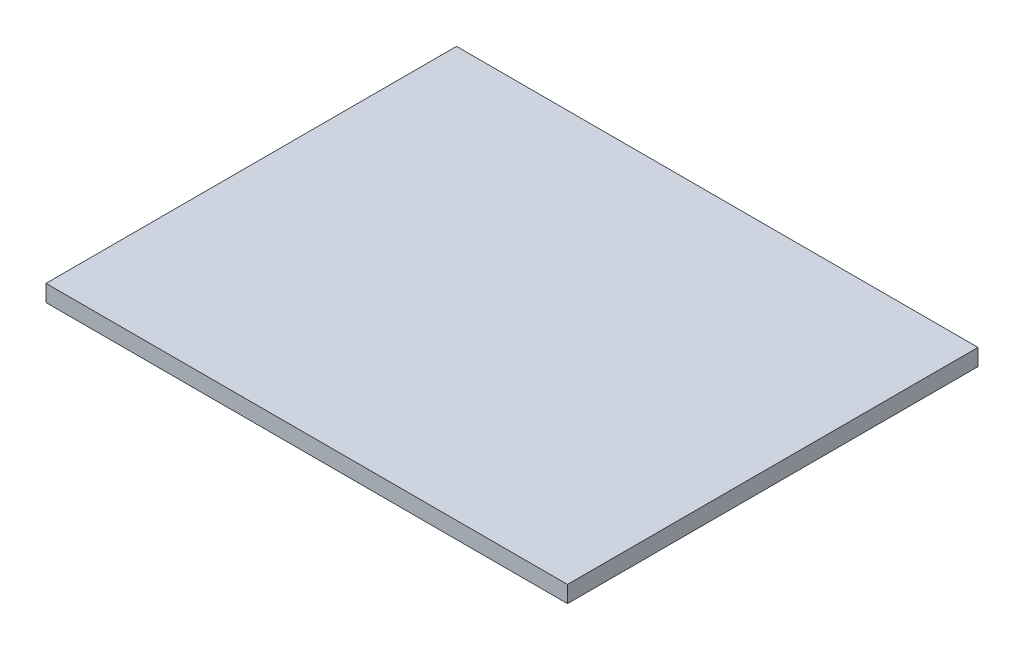
SolidWorks part; units mm, degrees
ref_plane "Front Plane" through (0, 0, 0) normal (0, 0, 1) x (1, 0, 0)
ref_plane "Top Plane" through (0, 0, 0) normal (0, 1, 0) x (1, 0, 0)
ref_plane "Right Plane" through (0, 0, 0) normal (1, 0, 0) x (0, 0, -1)
sketch "Sketch1" plane through (0, 0, 0) normal (0, 1, 0) x (1, 0, 0)
  line L1 (-47, 37) -> (47, 37)
  line L2 (-47, 37) -> (-47, -37)
  line L3 (-47, -37) -> (47, -37)
  line L4 (47, 37) -> (47, -37)
  line L5 (-47, 37) -> (47, -37) construction
  line L6 (-47, -37) -> (47, 37) construction
  point P0 (0, 0)
  dimension "D1" = 74
  dimension "D2" = 94
extrude "Boss-Extrude1" add sketch "Sketch1" along normal blind 3
